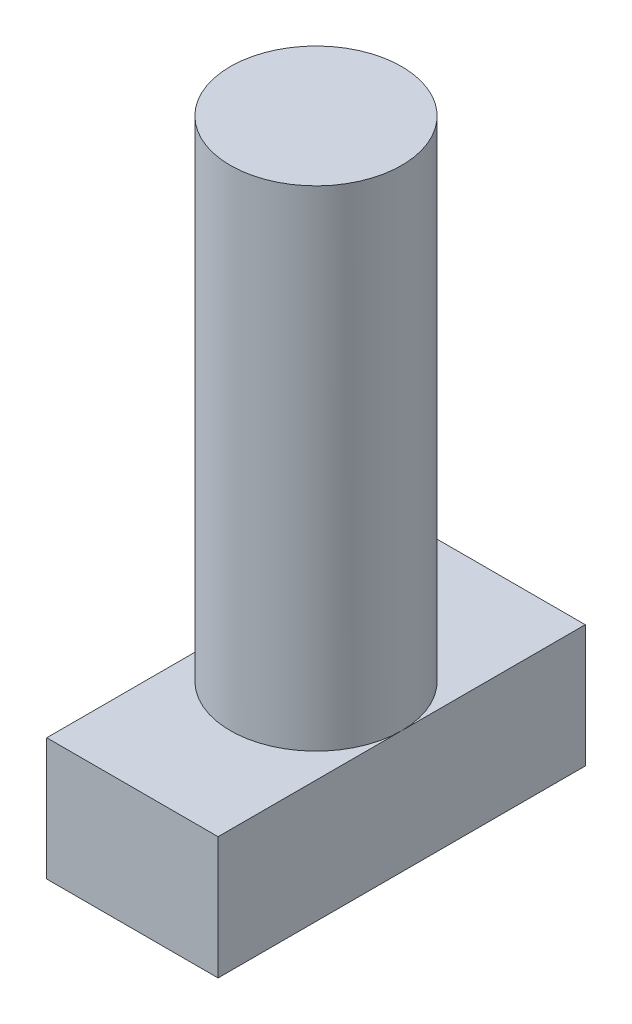
SolidWorks part; units mm, degrees
ref_plane "Front Plane" through (0, 0, 0) normal (0, 0, 1) x (1, 0, 0)
ref_plane "Top Plane" through (0, 0, 0) normal (0, 1, 0) x (1, 0, 0)
ref_plane "Right Plane" through (0, 0, 0) normal (1, 0, 0) x (0, 0, -1)
sketch "Sketch1" plane through (0, 0, 0) normal (0, 1, 0) x (1, 0, 0)
  line L1 (7, 15) -> (-7, 15)
  line L2 (7, 15) -> (7, -15)
  line L3 (7, -15) -> (-7, -15)
  line L4 (-7, 15) -> (-7, -15)
  line L5 (7, 15) -> (-7, -15) construction
  line L6 (7, -15) -> (-7, 15) construction
  point P0 (0, 0)
  dimension "D1" = 30
  dimension "D2" = 14
extrude "Boss-Extrude1" add sketch "Sketch1" along normal blind 10
sketch "Sketch2" plane through (0, 10, 0) normal (0, 1, 0) x (1, 0, 0)
  circle A0 centre (0, 0) radius 7
  dimension "D1" = 14
extrude "Boss-Extrude2" add sketch "Sketch2" along normal blind 40
